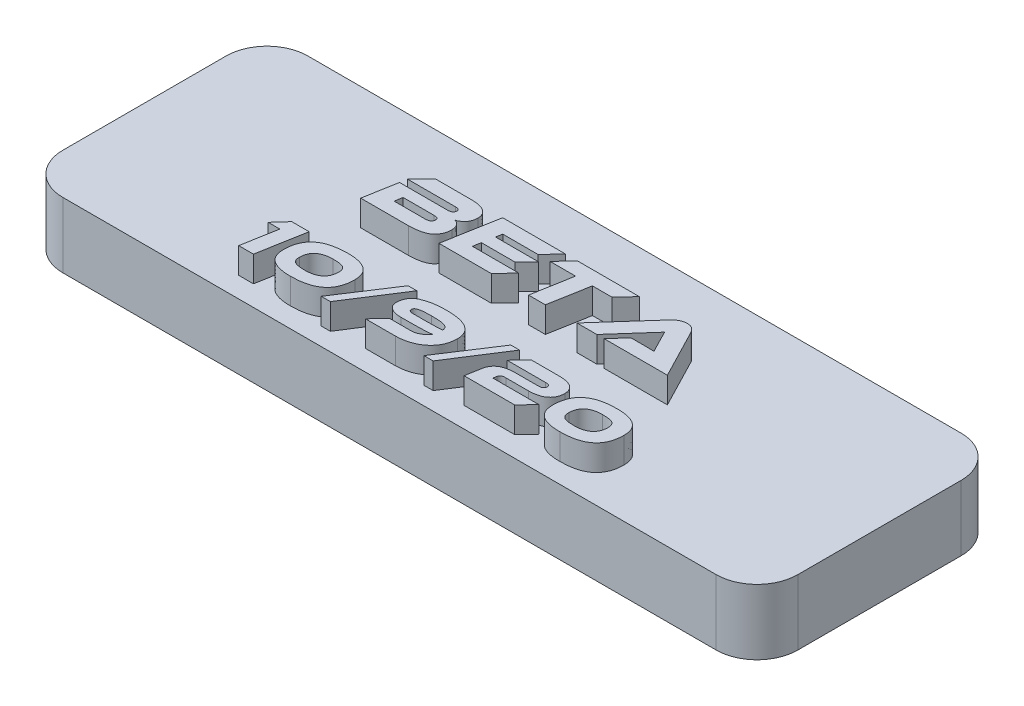
SolidWorks part; units mm, degrees
ref_plane "Front Plane" through (0, 0, 0) normal (0, 0, 1) x (1, 0, 0)
ref_plane "Top Plane" through (0, 0, 0) normal (0, 1, 0) x (1, 0, 0)
ref_plane "Right Plane" through (0, 0, 0) normal (1, 0, 0) x (0, 0, -1)
sketch "Sketch1" plane through (0, 0, 0) normal (0, 1, 0) x (1, 0, 0)
  line L1 (-28.575, 9.525) -> (28.575, 9.525)
  line L2 (-28.575, 9.525) -> (-28.575, -9.525)
  line L3 (-28.575, -9.525) -> (28.575, -9.525)
  line L4 (28.575, 9.525) -> (28.575, -9.525)
  line L5 (-28.575, 9.525) -> (28.575, -9.525) construction
  line L6 (-28.575, -9.525) -> (28.575, 9.525) construction
  point P0 (0, 0)
  dimension "D1" = 57.15
  dimension "D2" = 19.05
extrude "Boss-Extrude1" add sketch "Sketch1" along normal up to surface (5.08 mm away)
fillet "Fillet1" radius 3.175 4 edges at (-28.575, 2.54, 9.525) (-28.575, 2.54, -9.525) (28.575, 2.54, 9.525) (28.575, 2.54, -9.525)
sketch "Sketch3" plane through (0, 5.08, 0) normal (0, 1, 0) x (1, 0, 0)
  line L0 (28.575, -7.9375) -> (-28.575, -7.9375) construction
  line L1 (28.575, -6.35) -> (28.575, 6.35) construction
  line L2 (-28.575, 6.35) -> (-28.575, -6.35) construction
  line L3 (28.575, 0) -> (-28.575, 0) construction
  line L5 (-25.4, -9.525) -> (25.4, -9.525) construction
  line L6 (25.4, 9.525) -> (-25.4, 9.525) construction
  text T0 "Beta" font "Ethnocentric Rg" height in points 16
  text T1 "10/9/20\r\n" font "Ethnocentric Rg" height in points 14
  point P8 (-28.575, 0)
  dimension "D1" = 1.5875
extrude "Boss-Extrude2" add sketch "Sketch3" along normal blind 2
sketch "Sketch4" plane through (0, 0, 0) normal (0, -1, 0) x (1, 0, 0)
  line L0 (25.4, 0) -> (-25.4, 0) construction
  circle A0 centre (-25.4, 0) radius 0.9
  circle A1 centre (25.4, 0) radius 0.9
  point P3 (0, 0)
  dimension "D2" = 1.8
  dimension "D1" = 50.8
extrude "Cut-Extrude1" cut sketch "Sketch4" against normal blind 4
